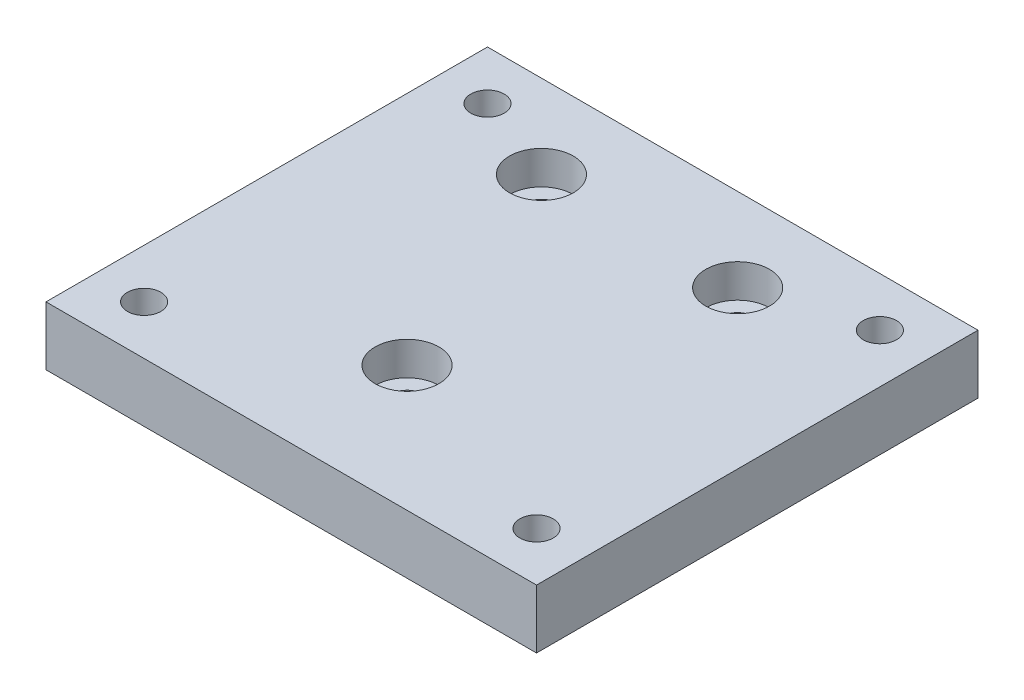
SolidWorks part; units mm, degrees
ref_plane "前视基准面" through (0, 0, 0) normal (0, 0, 1) x (1, 0, 0)
ref_plane "上视基准面" through (0, 0, 0) normal (0, 1, 0) x (1, 0, 0)
ref_plane "右视基准面" through (0, 0, 0) normal (1, 0, 0) x (0, 0, -1)
sketch "草图1" plane through (0, 0, 0) normal (0, 1, 0) x (1, 0, 0)
  line L1 (-25, 22.5) -> (25, 22.5)
  line L2 (-25, 22.5) -> (-25, -22.5)
  line L3 (-25, -22.5) -> (25, -22.5)
  line L4 (25, 22.5) -> (25, -22.5)
  line L5 (-25, 22.5) -> (25, -22.5) construction
  line L6 (-25, -22.5) -> (25, 22.5) construction
  point P0 (0, 0)
  dimension "D1" = 50
  dimension "D2" = 45
extrude "凸台-拉伸1" add sketch "草图1" along normal blind 6
sketch "草图2" plane through (0, 0, 0) normal (0, -1, 0) x (1, 0, 0)
  line L1 (-20, 17.5) -> (20, 17.5) construction
  line L2 (-20, 17.5) -> (-20, -17.5) construction
  line L3 (-20, -17.5) -> (20, -17.5) construction
  line L4 (20, 17.5) -> (20, -17.5) construction
  line L5 (-20, 17.5) -> (20, -17.5) construction
  line L6 (-20, -17.5) -> (20, 17.5) construction
  point P0 (0, 0)
  dimension "D1" = 40
  dimension "D2" = 35
hole_wizard "M3 六角凹头螺钉的柱形沉头孔1" positions "3D草图1" profile "草图3" counterbore size "M3" standard "ISO" end condition through all
sketch3d "3D草图1"
  point P0 (-20, 0, 17.5)
  point P3 (20, 0, 17.5)
  point P6 (20, 0, -17.5)
  point P9 (-20, 0, -17.5)
sketch "草图3" plane through (-20, 0, 17.5) normal (1, 0, 0) x (0, 0, -1)
  line L0 (0, 0) -> (0, 6)
  line L1 (0, 6) -> (1.7, 6)
  line L3 (1.7, 6) -> (1.7, 3.4)
  line L4 (1.7, 3.4) -> (3.25, 3.4)
  line L5 (3.25, 3.4) -> (3.25, 0)
  line L7 (3.25, 0) -> (0, 0)
  line L11 (0, -6.35) -> (0, 107.95) construction
  dimension "通孔孔直径" = 3.4
  dimension "通孔孔深度" = 6
  dimension "柱形沉头孔直径" = 6.5
  dimension "柱形沉头孔深度" = 3.4
sketch "草图4" plane through (0, 6, 0) normal (0, 1, 0) x (1, 0, 0)
  line L0 (-1, 14) -> (-1, -9.7) construction
  line L1 (-11, 14) -> (9, 14) construction
  circle A0 centre (-11, 14) radius 1.65
  circle A1 centre (9, 14) radius 1.65
  circle A2 centre (-1, -9.7) radius 1.65
  point P4 (0, 0)
  point P7 (-1, 14)
  dimension "D5" = 3.3
  dimension "D1" = 23.7
  dimension "D2" = 20
  dimension "D3" = 1
  dimension "D4" = 14
hole_wizard "M3 六角凹头螺钉的柱形沉头孔2" positions "3D草图2" profile "草图5" counterbore size "M3" standard "ISO" end condition through all
sketch3d "3D草图2"
  point P0 (-11, 6, -14)
  point P3 (9, 6, -14)
  point P6 (-1, 6, 9.7)
sketch "草图5" plane through (-11, 6, -14) normal (1, 0, 0) x (0, 0, 1)
  line L0 (0, 0) -> (0, 6)
  line L1 (0, 6) -> (1.7, 6)
  line L3 (1.7, 6) -> (1.7, 3.4)
  line L4 (1.7, 3.4) -> (3.25, 3.4)
  line L5 (3.25, 3.4) -> (3.25, 0)
  line L7 (3.25, 0) -> (0, 0)
  line L11 (0, -6.35) -> (0, 107.95) construction
  dimension "通孔孔直径" = 3.4
  dimension "通孔孔深度" = 6
  dimension "柱形沉头孔直径" = 6.5
  dimension "柱形沉头孔深度" = 3.4
